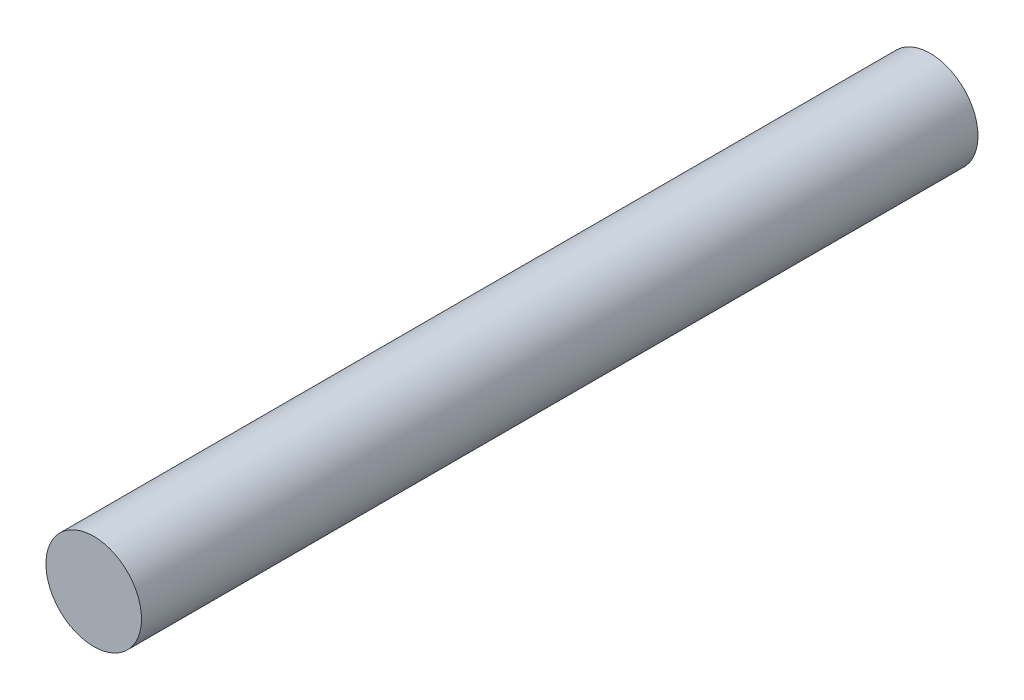
SolidWorks part; units mm, degrees
ref_plane "Ön Düzlem" through (0, 0, 0) normal (0, 0, 1) x (1, 0, 0)
ref_plane "Üst Düzlem" through (0, 0, 0) normal (0, 1, 0) x (1, 0, 0)
ref_plane "Sağ Düzlem" through (0, 0, 0) normal (1, 0, 0) x (0, 0, -1)
sketch "Sketch1" plane through (0, 0, 0) normal (0, 0, 1) x (1, 0, 0)
  circle A0 centre (0, 0) radius 4
extrude "Boss-Extrude1" add sketch "Sketch1" along normal blind 70
